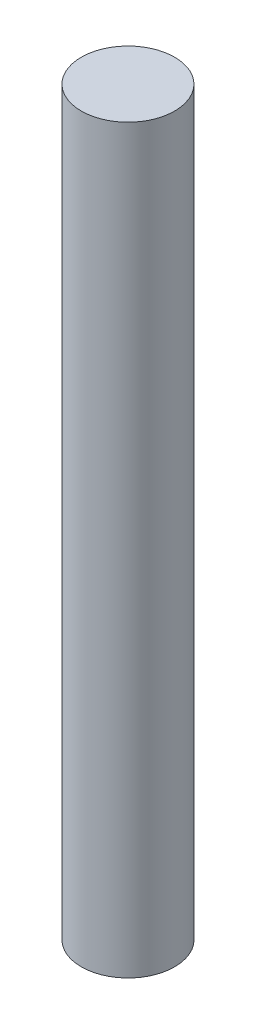
SolidWorks part; units mm, degrees
material "Cast Alloy Steel"
ref_plane "Front Plane" through (0, 0, 0) normal (0, 0, 1) x (1, 0, 0)
ref_plane "Top Plane" through (0, 0, 0) normal (0, 1, 0) x (1, 0, 0)
ref_plane "Right Plane" through (0, 0, 0) normal (1, 0, 0) x (0, 0, -1)
sketch "Sketch1" plane through (0, 0, 0) normal (0, 1, 0) x (1, 0, 0)
  circle A0 centre (0, 0) radius 4
  dimension "D1" = 8
extrude "Boss-Extrude1" add sketch "Sketch1" along normal blind 63.5
